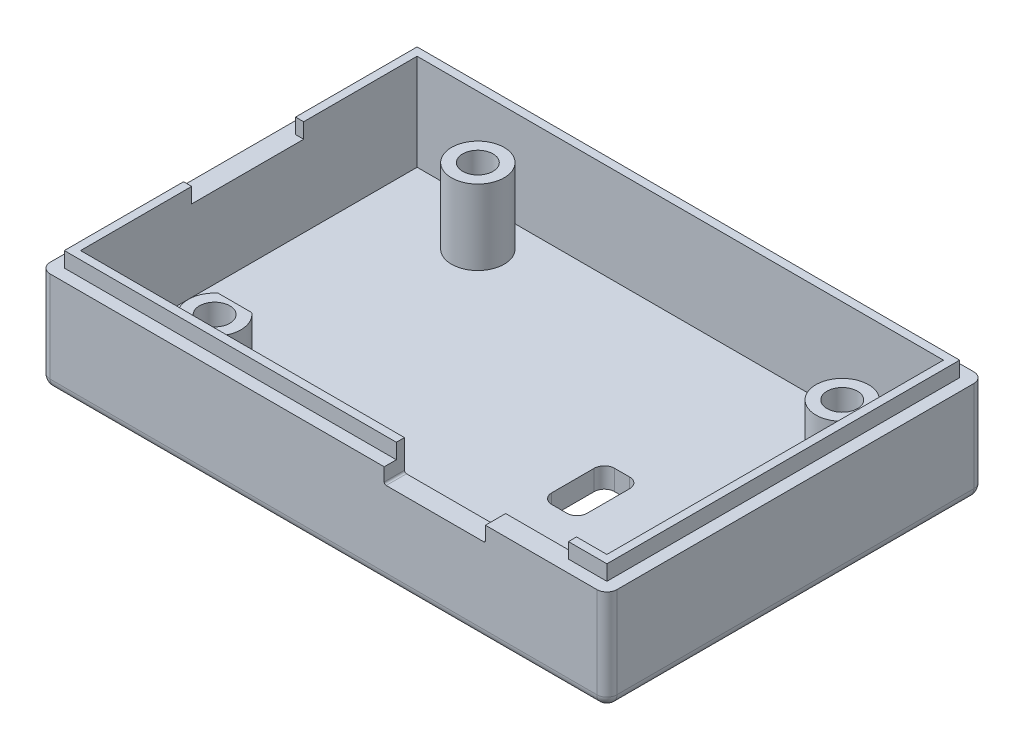
SolidWorks part; units mm, degrees
ref_plane "Front Plane" through (0, 0, 0) normal (0, 0, 1) x (1, 0, 0)
ref_plane "Top Plane" through (0, 0, 0) normal (0, 1, 0) x (1, 0, 0)
ref_plane "Right Plane" through (0, 0, 0) normal (1, 0, 0) x (0, 0, -1)
sketch "Sketch1" plane through (0, 0, 0) normal (0, 1, 0) x (1, 0, 0)
  line L0 (0, 0) -> (56, 0)
  line L1 (56, 0) -> (56, 37.25)
  line L2 (56, 37.25) -> (0, 37.25)
  line L3 (0, 37.25) -> (0, 0)
  dimension "D1" = 56
  dimension "D2" = 37.25
extrude "Boss-Extrude1" add sketch "Sketch1" along normal blind 2
sketch "Sketch2" plane through (0, 2, 0) normal (0, 1, 0) x (1, 0, 0)
  line L0 (2, 35.25) -> (2, 2)
  line L1 (2, 2) -> (54, 2)
  line L2 (0, 37.25) -> (0, 0) construction
  line L3 (0, 0) -> (56, 0) construction
  line L4 (2, 35.25) -> (54, 35.25)
  line L5 (54, 35.25) -> (54, 2)
  line L6 (56, 0) -> (56, 37.25) construction
  line L7 (56, 37.25) -> (0, 37.25) construction
  line L12 (0, 37.25) -> (0, 0)
  line L13 (0, 0) -> (56, 0)
  line L14 (56, 0) -> (56, 37.25)
  line L15 (56, 37.25) -> (0, 37.25)
  line L16 (0, 37.25) -> (0, 0)
  line L17 (0, 0) -> (56, 0)
  line L18 (56, 0) -> (56, 37.25)
  line L19 (56, 37.25) -> (0, 37.25)
  dimension "D1" = 2
  dimension "D2" = 2
  dimension "D3" = 2
  dimension "D4" = 2
  dimension "D5" = 0
extrude "Boss-Extrude2" add sketch "Sketch2" along normal blind 9
sketch "Sketch3" plane through (0, 2, 0) normal (0, 1, 0) x (1, 0, 0)
  line L0 (54, 2) -> (54, 35.25) construction
  line L1 (54, 35.25) -> (2, 35.25) construction
  line L2 (12, 5.25) -> (12, 31.25) construction
  line L3 (12, 31.25) -> (48, 31.25) construction
  circle A0 centre (12, 5.25) radius 2.6
  circle A1 centre (12, 31.25) radius 2.6
  circle A2 centre (48, 31.25) radius 2.6
  circle A3 centre (12, 5.25) radius 1.5
  circle A4 centre (12, 31.25) radius 1.5
  circle A5 centre (48, 31.25) radius 1.5
  dimension "D1" = 26
  dimension "D2" = 6
  dimension "D3" = 36
  dimension "D4" = 4
extrude "Boss-Extrude3" add sketch "Sketch3" along normal blind 7.4
sketch "Sketch4" plane through (0, 2, 0) normal (0, 1, 0) x (1, 0, 0)
  circle A0 centre (12, 5.25) radius 1.5 construction
  circle A1 centre (48, 31.25) radius 1.5 construction
  circle A2 centre (12, 31.25) radius 1.5 construction
  circle A3 centre (12, 5.25) radius 1.5
  circle A4 centre (48, 31.25) radius 1.5
  circle A5 centre (12, 31.25) radius 1.5
extrude "Boss-Extrude4" [suppressed] add sketch "Sketch4" along normal blind 3.4
sketch "Sketch5" plane through (0, 11, 0) normal (0, 1, 0) x (1, 0, 0)
  line L0 (1.2, 1.2) -> (54.8, 1.2)
  line L1 (0, 0) -> (56, 0) construction
  line L2 (54.8, 1.2) -> (54.8, 36.05)
  line L3 (54.8, 36.05) -> (1.2, 36.05)
  line L4 (1.2, 36.05) -> (1.2, 1.2)
  line L5 (56, 0) -> (56, 37.25) construction
  line L6 (56, 37.25) -> (0, 37.25) construction
  line L7 (0, 37.25) -> (0, 0) construction
  line L8 (0, 37.25) -> (0, 0)
  line L9 (56, 37.25) -> (0, 37.25)
  line L10 (56, 0) -> (56, 37.25)
  line L11 (0, 0) -> (56, 0)
  dimension "D1" = 1.2
  dimension "D2" = 1.2
  dimension "D3" = 1.2
  dimension "D4" = 1.2
extrude "Cut-Extrude1" cut sketch "Sketch5" against normal blind 1
sketch "Sketch6" [suppressed] plane through (0, 5.4, 0) normal (0, 1, 0) x (1, 0, 0)
  circle A0 centre (12, 5.25) radius 1
  circle A1 centre (12, 31.25) radius 1
  circle A2 centre (48, 31.25) radius 1
  circle A3 centre (48, 31.25) radius 1.5 construction
  circle A4 centre (12, 31.25) radius 1.5 construction
  circle A5 centre (12, 5.25) radius 1.5 construction
  circle A6 centre (48, 31.25) radius 1.5
  circle A7 centre (12, 31.25) radius 1.5
  circle A8 centre (12, 5.25) radius 1.5
extrude "Boss-Extrude5" [suppressed] add sketch "Sketch6" along normal blind 5
fillet "Fillet1" radius 1 4 edges at (56, 5, -37.25) (56, 5, 0) (0, 5, -37.25) (0, 5, 0)
sketch "Sketch7" plane through (0, 2, 0) normal (0, 1, 0) x (1, 0, 0)
  circle A0 centre (12, 5.25) radius 1.5 construction
  circle A1 centre (48, 31.25) radius 1.5 construction
  circle A2 centre (12, 31.25) radius 1.5 construction
  circle A3 centre (12, 5.25) radius 1.5
  circle A4 centre (48, 31.25) radius 1.5
  circle A5 centre (12, 31.25) radius 1.5
extrude "Cut-Extrude2" cut sketch "Sketch7" against normal blind 10
sketch "Sketch8" plane through (0, 0, 0) normal (0, 0, 1) x (1, 0, 0)
  line L0 (44, 10) -> (44, 8.5)
  line L1 (1, 10) -> (55, 10) construction
  line L2 (34, 10) -> (34, 8.5)
  line L3 (34, 8.5) -> (44, 8.5)
  line L4 (34, 12.3) -> (34, 10) construction
  line L6 (34, 10) -> (44, 10) construction
  line L7 (34, 10) -> (34, 11)
  line L8 (34, 11) -> (44, 11)
  line L9 (44, 11) -> (44, 10)
  line L10 (1.2, 11) -> (54.8, 11) construction
  dimension "D1" = 2.5
extrude "Cut-Extrude3" cut sketch "Sketch8" against normal blind 3
fillet "Fillet2" radius 1 8 edges at (55.7071, 0, -0.2929) (28, 0, 0) (0.2929, 0, -0.2929) (0, 0, -18.625) (0.2929, 0, -36.9571) (28, 0, -37.25) (55.7071, 0, -36.9571) (56, 0, -18.625)
sketch "Sketch9" plane through (0, 9.4, 0) normal (0, 1, 0) x (1, 0, 0)
  line L0 (12, 5.25) -> (12, 7.25) construction
  line L1 (12, 7.25) -> (13.6613, 7.25)
  line L2 (12, 7.25) -> (10.3387, 7.25)
  circle A0 centre (12, 5.25) radius 2.6 construction
  arc A1 (13.6613, 7.25) -> (10.3387, 7.25) centre (12, 5.25) ccw
extrude "Cut-Extrude4" cut sketch "Sketch9" against normal up to surface (7.4 mm away) up to face at (48, 2, -28.65)
sketch "Sketch10" plane through (0, 2, 0) normal (0, 1, 0) x (1, 0, 0)
  line L0 (54, 2) -> (54, 35.25) construction
  line L1 (36.5, 19.25) -> (40, 19.25)
  line L2 (36.5, 19.25) -> (36.5, 13.05)
  line L3 (36.5, 13.05) -> (40, 13.05)
  line L4 (40, 19.25) -> (40, 13.05)
  line L5 (54, 35.25) -> (2, 35.25) construction
  point P4 (38.25, 13.05)
  dimension "D1" = 3.5
  dimension "D2" = 6.2
  dimension "D3" = 14
  dimension "D4" = 16
extrude "Cut-Extrude5" cut sketch "Sketch10" against normal blind 10
fillet "Fillet3" radius 1 4 edges at (40, 1, -13.05) (36.5, 1, -13.05) (40, 1, -19.25) (36.5, 1, -19.25)
sketch "Sketch11" plane through (0, 0, -1.2) normal (0, 0, 1) x (1, 0, 0)
  line L0 (51, 11) -> (51, 10)
  line L4 (44, 11) -> (44, 10)
  line L5 (44, 10) -> (54.8, 10)
  line L6 (54.8, 10) -> (54.8, 11)
  line L7 (54.8, 11) -> (44, 11)
  line L8 (44, 11) -> (44, 10)
  line L9 (44, 10) -> (51, 10)
  line L11 (51, 11) -> (44, 11)
  point P6 (44, 10.5)
  point P7 (51, 10.5)
  dimension "D2" = 7
  dimension "D1" = 0
extrude "Cut-Extrude6" cut sketch "Sketch11" against normal blind 10
fillet "Fillet4" radius 0.2 2 edges at (44, 8.5, -1) (34, 8.5, -1)
sketch "Sketch12" plane through (0, 11, 0) normal (0, 1, 0) x (1, 0, 0)
  line L12 (51, 2) -> (51, 1.2)
  line L13 (51, 1.2) -> (54.8, 1.2)
  line L14 (54.8, 1.2) -> (54.8, 36.05)
  line L15 (54.8, 36.05) -> (1.2, 36.05)
  line L16 (1.2, 36.05) -> (1.2, 1.2)
  line L17 (1.2, 1.2) -> (34, 1.2)
  line L18 (34, 1.2) -> (34, 2)
  line L19 (34, 2) -> (2, 2)
  line L20 (2, 2) -> (2, 35.25)
  line L21 (2, 35.25) -> (54, 35.25)
  line L22 (54, 35.25) -> (54, 2)
  line L23 (54, 2) -> (51, 2)
  line L24 (51, 2) -> (51, 1.2)
  line L25 (51, 1.2) -> (54.8, 1.2)
  line L26 (54.8, 1.2) -> (54.8, 36.05)
  line L27 (54.8, 36.05) -> (1.2, 36.05)
  line L28 (1.2, 36.05) -> (1.2, 1.2)
  line L29 (1.2, 1.2) -> (34, 1.2)
  line L30 (34, 1.2) -> (34, 2)
  line L31 (34, 2) -> (2, 2)
  line L32 (2, 2) -> (2, 35.25)
  line L33 (2, 35.25) -> (54, 35.25)
  line L34 (54, 35.25) -> (54, 2)
  line L35 (54, 2) -> (51, 2)
  dimension "D1" = 0
extrude "Boss-Extrude6" add sketch "Sketch12" along normal blind 0.5
sketch "Sketch13" plane through (1.2, 0, 0) normal (-1, 0, 0) x (0, 0, 1)
  line L0 (-12.98, 11.5) -> (-12.98, 10)
  line L1 (-36.05, 11.5) -> (-1.2, 11.5) construction
  line L2 (-36.05, 10) -> (-1.2, 10) construction
  line L3 (0, 10) -> (0, 1) construction
  line L4 (-12.98, 11.5) -> (-24.0434, 11.5)
  line L5 (-24.0434, 11.5) -> (-24.0434, 10)
  line L6 (-24.0434, 10) -> (-12.98, 10)
  dimension "D1" = 12.98
  dimension "D2" = 11.0634
extrude "Cut-Extrude9" cut sketch "Sketch13" against normal blind 2
sketch "Sketch14" plane through (0, 9.4, 0) normal (0, 1, 0) x (1, 0, 0)
  circle A1 centre (48, 31.25) radius 2.6
  circle A2 centre (48, 31.25) radius 2.6
  dimension "D1" = 0
extrude "Cut-Extrude10" cut sketch "Sketch14" against normal blind 2.3
